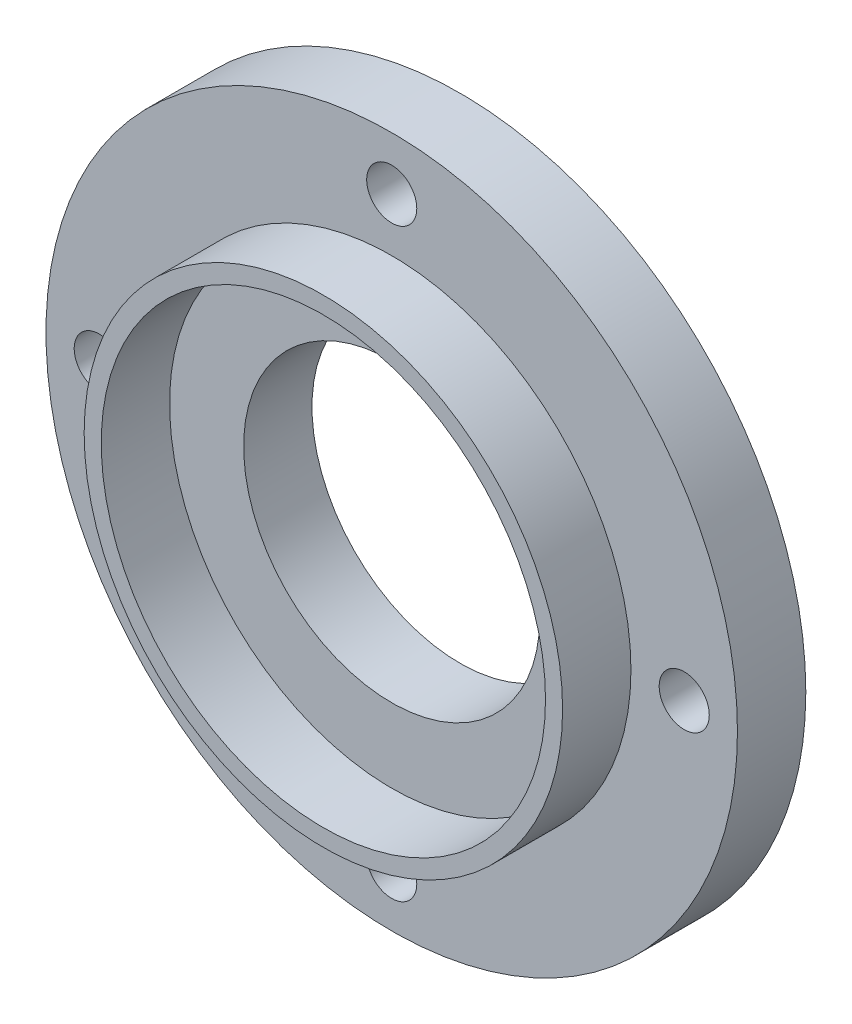
SolidWorks part; units mm, degrees
material "Hexcel AS4C (3000 Filaments)"
ref_plane "Front Plane" through (0, 0, 0) normal (0, 0, 1) x (1, 0, 0)
ref_plane "Top Plane" through (0, 0, 0) normal (0, 1, 0) x (1, 0, 0)
ref_plane "Right Plane" through (0, 0, 0) normal (1, 0, 0) x (0, 0, -1)
sketch "Sketch1" plane through (0, 0, 0) normal (0, 0, 1) x (1, 0, 0)
  circle A1 centre (0, 0) radius 15.175
  circle A2 centre (0, 0) radius 6.5
  dimension "D1" = 30.35
  dimension "D2" = 13
extrude "Boss-Extrude1" add sketch "Sketch1" along normal blind 3
sketch "Sketch2" plane through (0, 0, 3) normal (0, 0, 1) x (1, 0, 0)
  circle A0 centre (0, 0) radius 9.75
  circle A1 centre (0, 0) radius 10.5
  dimension "D1" = 19.5
  dimension "D2" = 21
extrude "Boss-Extrude2" add sketch "Sketch2" along normal blind 3
sketch "Sketch3" plane through (0, 0, 0) normal (0, 0, -1) x (-1, 0, 0)
  circle A0 centre (0, 0) radius 12.8375 construction
  circle A1 centre (0, 0) radius 12.8375 construction
  point P3 (0, 12.8375)
  point P4 (-12.8375, 0)
  point P5 (0, -12.8375)
  point P6 (12.8375, 0)
hole_wizard "M2 Clearance Hole1" positions "Sketch4" profile "Sketch5" hole size "M2" standard "ANSI Metric"
sketch "Sketch4" plane through (0, 0, 0) normal (0, 0, -1) x (-1, 0, 0)
  point P0 (0, 12.8375)
  point P3 (12.8375, 0)
  point P6 (0, -12.8375)
  point P9 (-12.8375, 0)
sketch "Sketch5" plane through (0, 12.8375, 0) normal (1, 0, 0) x (0, 1, 0)
  line L0 (0, 0) -> (0, 10.6609)
  line L1 (0, 10.6609) -> (1.1, 10)
  line L2 (1.1, 10) -> (1.1, 0)
  line L5 (1.1, 0) -> (0, 0)
  line L10 (0, 10.6609) -> (-1.1, 10) construction
  line L11 (0, -6.35) -> (0, 107.95) construction
  dimension "Hole Dia." = 2.2
  dimension "Hole Depth" = 10
  dimension "Drill Angle" = 118
equation "\"tubeOutDiameter\" = 35mm"
equation "\"wheelShaftDiameter\"= 12mm"
equation "\"wheelThickness\"= 135mm"
equation "\"BearingDiameter\"= 20mm"
equation "\"BearingThickness\"= 10mm"
equation "\"frontShaftDiameter\"= 20mm"
equation "\"D1@Sketch1\"=\"wheelShaftDiameter\"*2+0.25in"
equation "\"D2@Sketch1\"=\"wheelShaftDiameter\"+1mm"
